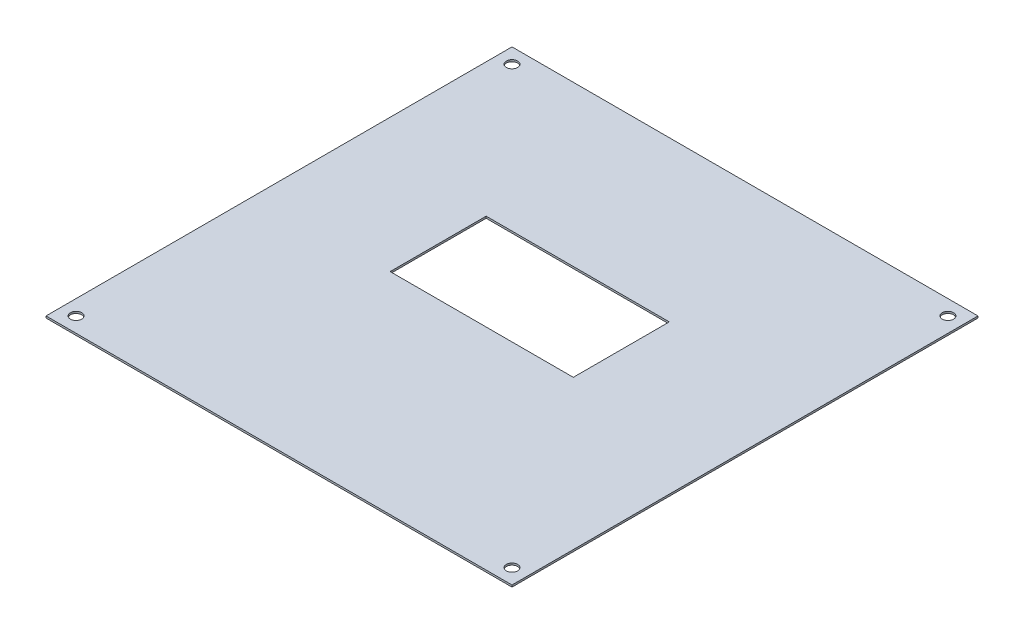
SolidWorks part; units mm, degrees
ref_plane "Спереди" through (0, 0, 0) normal (0, 0, 1) x (1, 0, 0)
ref_plane "Сверху" through (0, 0, 0) normal (0, 1, 0) x (1, 0, 0)
ref_plane "Справа" through (0, 0, 0) normal (1, 0, 0) x (0, 0, -1)
sketch "Эскиз1" plane through (0, 0, 0) normal (0, 1, 0) x (1, 0, 0)
  line L1 (0, 0) -> (124, 0)
  line L2 (0, 0) -> (0, 124)
  line L3 (0, 124) -> (124, 124)
  line L4 (124, 0) -> (124, 124)
  line L5 (35.5689, 81.5531) -> (84.3043, 81.5531)
  line L6 (35.5689, 81.5531) -> (35.5689, 56.0063)
  line L7 (35.5689, 56.0063) -> (84.3043, 56.0063)
  line L8 (84.3043, 81.5531) -> (84.3043, 56.0063)
  circle A0 centre (4, 120) radius 1.5
  circle A1 centre (120, 120) radius 1.5
  circle A2 centre (120, 4) radius 1.5
  circle A3 centre (4, 4) radius 1.5
  dimension "D3" = 3
  dimension "D4" = 3
  dimension "D5" = 3
  dimension "D6" = 3
  dimension "D1" = 124
  dimension "D2" = 124
  dimension "D7" = 4
  dimension "D8" = 4
  dimension "D9" = 4
  dimension "D10" = 4
  dimension "D11" = 4
  dimension "D12" = 4
  dimension "D13" = 4
  dimension "D14" = 4
extrude "Бобышка-Вытянуть1" add sketch "Эскиз1" along normal blind 0.5
equation "\"D9@Эскиз1\"=\"D7@Эскиз1\""
equation "\"D10@Эскиз1\"=\"D9@Эскиз1\""
equation "\"0ю5\"=10"
